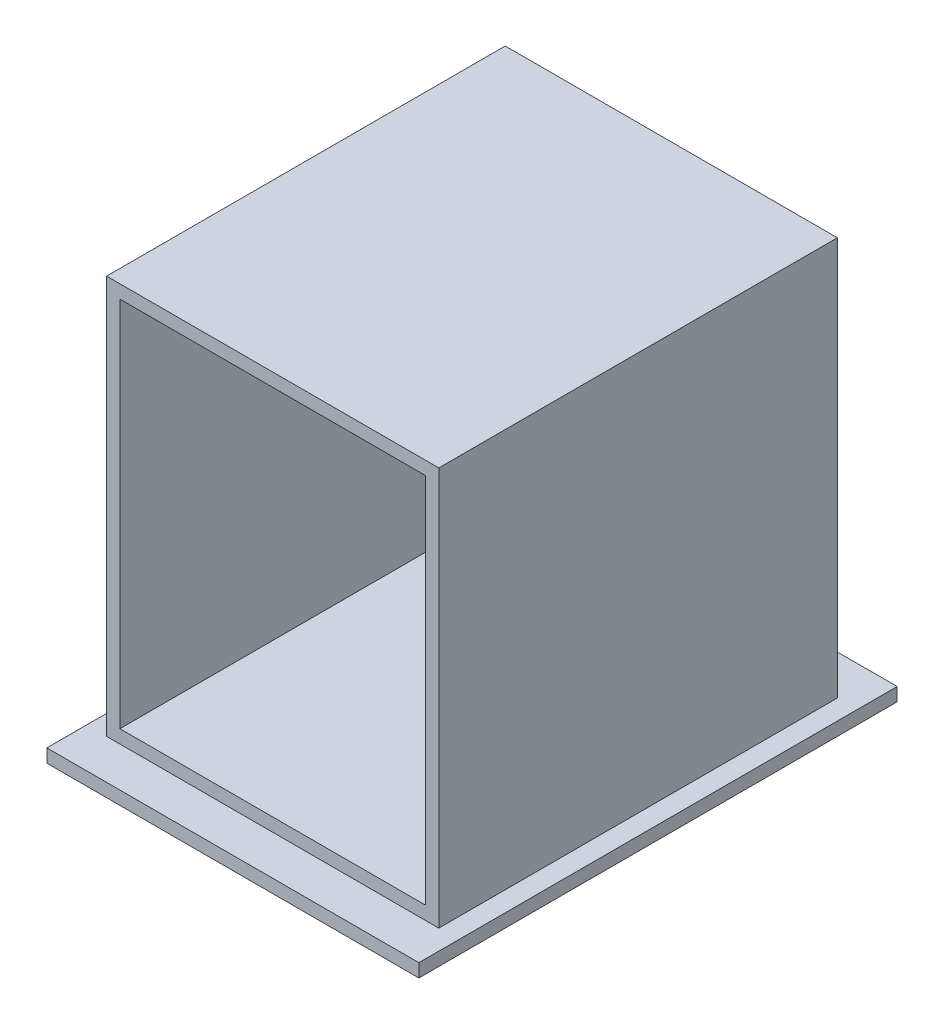
SolidWorks part; units mm, degrees
ref_plane "前视基准面" through (0, 0, 0) normal (0, 0, 1) x (1, 0, 0)
ref_plane "上视基准面" through (0, 0, 0) normal (0, 1, 0) x (1, 0, 0)
ref_plane "右视基准面" through (0, 0, 0) normal (1, 0, 0) x (0, 0, -1)
sketch "草图1" plane through (0, 0, 0) normal (0, 0, 1) x (1, 0, 0)
  line L1 (0, 0) -> (250, 0)
  line L2 (0, 0) -> (0, 300)
  line L3 (0, 300) -> (250, 300)
  line L4 (250, 0) -> (250, 300)
  dimension "D1" = 250
  dimension "D2" = 300
extrude "凸台-拉伸1" add sketch "草图1" along normal blind 300
sketch "草图2" plane through (0, 0, 300) normal (0, 0, 1) x (1, 0, 0)
  line L0 (250, 0) -> (250, 300) construction
  line L1 (10, 10) -> (240, 10)
  line L2 (10, 10) -> (10, 290)
  line L3 (10, 290) -> (240, 290)
  line L4 (240, 10) -> (240, 290)
  line L5 (250, 300) -> (0, 300) construction
  line L6 (0, 300) -> (0, 0) construction
  line L7 (0, 0) -> (250, 0) construction
  dimension "D1" = 10
  dimension "D2" = 10
  dimension "D3" = 10
  dimension "D4" = 10
extrude "切除-拉伸1" cut sketch "草图2" against normal blind 290
sketch "草图3" plane through (0, 0, 0) normal (0, -1, 0) x (1, 0, 0)
  line L0 (250, 300) -> (250, 0) construction
  line L1 (-15, 330) -> (265, 330)
  line L2 (-15, 330) -> (-15, -30)
  line L3 (-15, -30) -> (265, -30)
  line L4 (265, 330) -> (265, -30)
  line L5 (0, 300) -> (0, 0) construction
  line L6 (0, 300) -> (250, 300) construction
  line L7 (0, 0) -> (250, 0) construction
  dimension "D1" = 15
  dimension "D2" = 15
  dimension "D3" = 30
  dimension "D4" = 30
extrude "凸台-拉伸2" add sketch "草图3" along normal blind 10
sketch "草图4" plane through (0, -10, 0) normal (0, -1, 0) x (1, 0, 0)
  line L0 (92.0112, 270) -> (173.3456, 270) construction
  line L1 (92.0112, 284.2193) -> (173.3456, 284.2193)
  line L2 (92.0112, 255.7807) -> (173.3456, 255.7807)
  line L3 (265, 330) -> (-15, 330) construction
  arc A0 (92.0112, 284.2193) -> (92.0112, 255.7807) centre (92.0112, 270) ccw
  arc A1 (173.3456, 255.7807) -> (173.3456, 284.2193) centre (173.3456, 270) ccw
  point P2 (132.6784, 270)
  dimension "D1" = 60
extrude "切除-拉伸2" cut sketch "草图4" against normal blind 10
